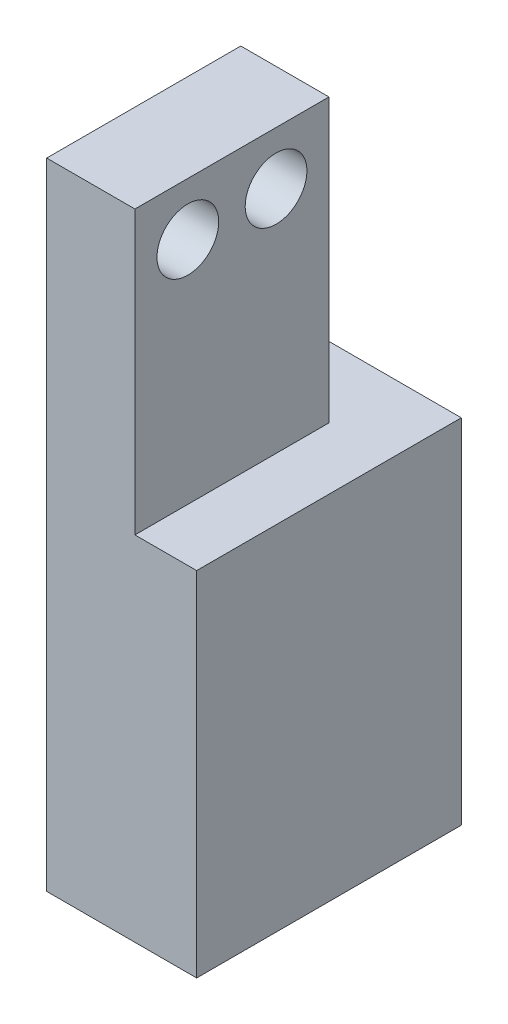
SolidWorks part; units mm, degrees
material "ABS"
ref_plane "Front Plane" through (0, 0, 0) normal (0, 0, 1) x (1, 0, 0)
ref_plane "Top Plane" through (0, 0, 0) normal (0, 1, 0) x (1, 0, 0)
ref_plane "Right Plane" through (0, 0, 0) normal (1, 0, 0) x (0, 0, -1)
sketch "Sketch1" plane through (0, 0, 0) normal (0, 0, 1) x (1, 0, 0)
  line L0 (0, 36) -> (0, 0)
  line L1 (0, 0) -> (8.5, 0)
  line L2 (8.5, 0) -> (8.5, 20)
  line L3 (8.5, 20) -> (5, 20)
  line L4 (5, 20) -> (5, 36)
  line L5 (5, 36) -> (0, 36)
  dimension "D1" = 5
  dimension "D2" = 16
  dimension "D3" = 20
  dimension "D4" = 8.5
extrude "Boss-Extrude1" add sketch "Sketch1" against normal blind 15
sketch "Sketch2" plane through (0, 36, 0) normal (0, 1, 0) x (1, 0, 0)
  line L5 (5, 15) -> (5, 0) construction
  line L6 (0, 15) -> (5, 15)
  line L7 (0, 15) -> (0, 11)
  line L8 (0, 11) -> (5, 11)
  line L9 (5, 15) -> (5, 11)
  dimension "D1" = 4
  dimension "D2" = 5
extrude "Cut-Extrude1" cut sketch "Sketch2" against normal up to surface (16 mm away) up to face at (6.75, 20, -7.5)
sketch "Sketch7" plane through (5, 0, 0) normal (1, 0, 0) x (0, 0, -1)
  line L1 (0, 36) -> (11, 36) construction
  line L2 (0, 20) -> (0, 36) construction
  circle A0 centre (3, 33) radius 1.75
  circle A1 centre (8, 33) radius 1.75
  dimension "D1" = 3.5
  dimension "D2" = 5
  dimension "D3" = 3
  dimension "D4" = 3
extrude "Cut-Extrude3" cut sketch "Sketch7" against normal through all
